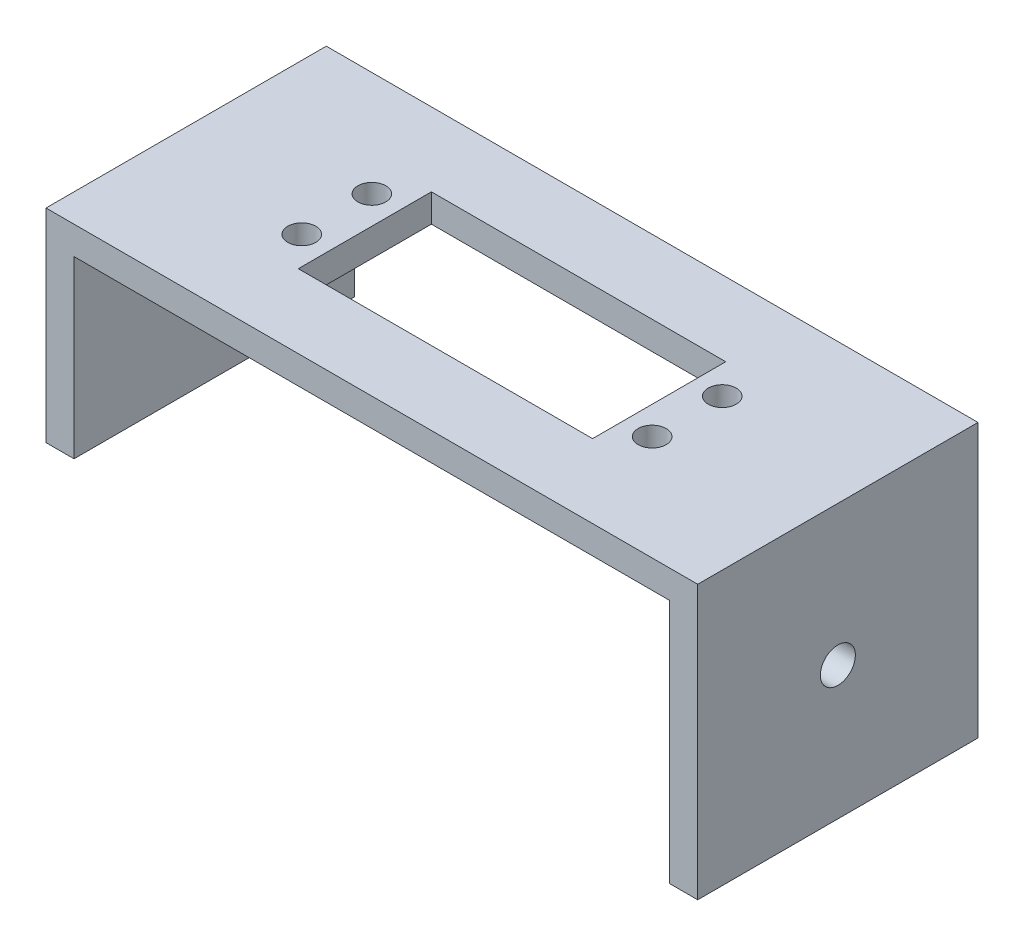
SolidWorks part; units mm, degrees
ref_plane "Alzado" through (0, 0, 0) normal (0, 0, 1) x (1, 0, 0)
ref_plane "Planta" through (0, 0, 0) normal (0, 1, 0) x (1, 0, 0)
ref_plane "Vista lateral" through (0, 0, 0) normal (1, 0, 0) x (0, 0, -1)
sketch "Croquis2" plane through (0, 0, 0) normal (0, 0, 1) x (1, 0, 0)
  line L0 (-40.0265, 0) -> (59.1402, 0) construction
  line L1 (-31.1459, -11.0012) -> (-31.1459, 23.9988)
  line L2 (-31.1459, 23.9988) -> (53.8541, 23.9988)
  line L3 (53.8541, 23.9988) -> (53.8541, -11.0012)
  line L4 (-31.1459, -11.0012) -> (-35.1459, -11.0012)
  line L5 (-35.1459, -11.0012) -> (-35.1459, 27.9988)
  line L6 (53.8541, -11.0012) -> (57.8541, -11.0012)
  line L7 (57.8541, -11.0012) -> (57.8541, 27.9988)
  line L8 (57.8541, 27.9988) -> (-35.1459, 27.9988)
  dimension "D1" = 85
  dimension "D2" = 35
  dimension "D3" = 35
  dimension "D4" = 4
  dimension "D5" = 39
  dimension "D6" = 4
extrude "Saliente-Extruir1" add sketch "Croquis2" along normal blind 40
sketch "Croquis3" plane through (-35.1459, 0, 0) normal (-1, 0, 0) x (0, 0, 1)
  line L0 (40, 27.9988) -> (0, 27.9988) construction
  circle A0 centre (20, 7.9988) radius 2.5
  dimension "D1" = 5
  dimension "D2" = 25
extrude "Cortar-Extruir1" cut sketch "Croquis3" against normal through all
sketch "Croquis5" plane through (-35.1459, 0, 0) normal (-1, 0, 0) x (0, 0, 1)
  line L0 (0, 27.9988) -> (0, -11.0012) construction
  line L1 (40, -11.0012) -> (0, -11.0012)
  line L2 (40, -11.0012) -> (40, -1.0012)
  line L3 (40, -1.0012) -> (0, -1.0012)
  line L4 (0, -11.0012) -> (0, -1.0012)
  dimension "D1" = 10
extrude "Cortar-Extruir2" cut sketch "Croquis5" against normal blind 40
sketch "Croquis6" plane through (0, 27.9988, 0) normal (0, 1, 0) x (1, 0, 0)
  line L0 (-35.1459, -40) -> (-35.1459, 0) construction
  line L1 (-9.6459, -10.5) -> (32.3541, -10.5)
  line L2 (-9.6459, -10.5) -> (-9.6459, -29.5)
  line L3 (-9.6459, -29.5) -> (32.3541, -29.5)
  line L4 (32.3541, -10.5) -> (32.3541, -29.5)
  line L5 (-9.6459, -10.5) -> (32.3541, -29.5) construction
  line L6 (-9.6459, -29.5) -> (32.3541, -10.5) construction
  point P0 (11.3541, -20)
  point P10 (-35.1459, -20)
  dimension "D1" = 42
  dimension "D2" = 46.5
  dimension "D3" = 19
extrude "Cortar-Extruir3" cut sketch "Croquis6" against normal blind 10
sketch "Croquis7" plane through (0, 27.9988, 0) normal (0, 1, 0) x (1, 0, 0)
  line L0 (-15.6459, 6.5811) -> (-15.6459, -45.5911) construction
  line L1 (-9.6459, -10.5) -> (-9.6459, -29.5) construction
  line L2 (-9.6459, -20) -> (32.3541, -20) construction
  line L3 (38.3541, 7.3731) -> (38.3541, -50.5411) construction
  line L4 (32.3541, -29.5) -> (32.3541, -10.5) construction
  circle A0 centre (-13.6459, -15) radius 2
  circle A1 centre (-13.6459, -25) radius 2
  circle A2 centre (36.3541, -15) radius 2
  circle A3 centre (36.3541, -25) radius 2
  point P20 (0, 0)
  point P21 (0, 0)
  point P22 (0, 0)
  dimension "D1" = 4
  dimension "D2" = 4
  dimension "D3" = 4
  dimension "D4" = 4
  dimension "D5" = 4
  dimension "D6" = 4
  dimension "D7" = 5
  dimension "D8" = 5
  dimension "D9" = 5
  dimension "D10" = 5
  dimension "D11" = 6
  dimension "D12" = 6
extrude "Cortar-Extruir4" cut sketch "Croquis7" against normal blind 10
